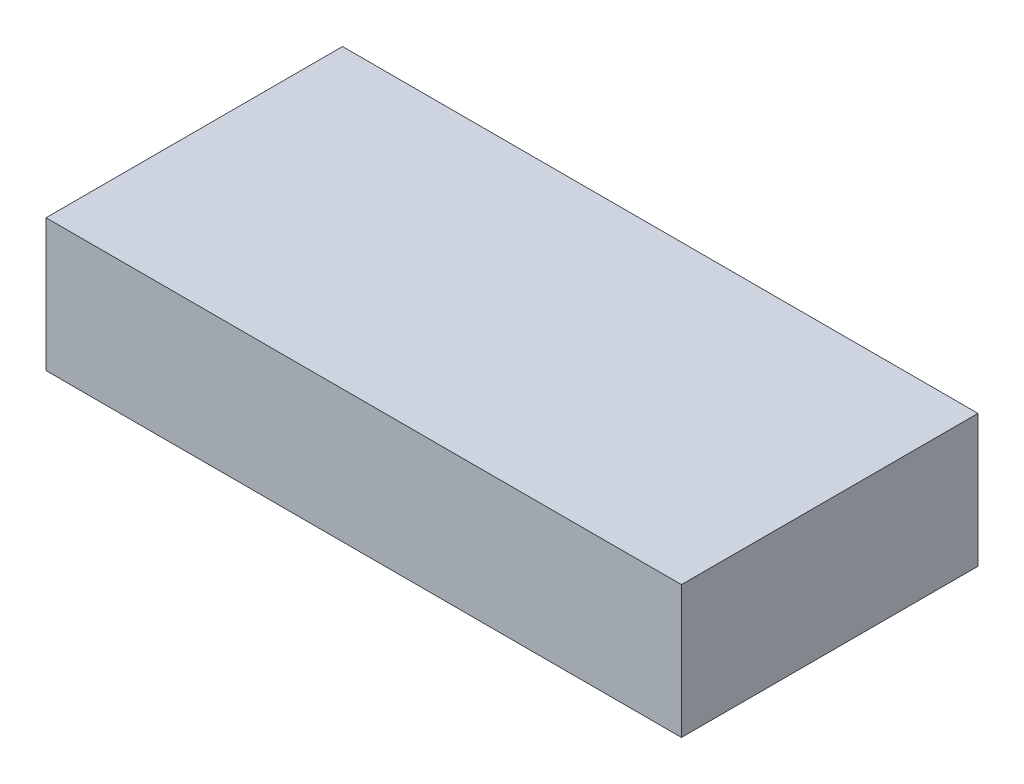
SolidWorks part; units mm, degrees
ref_plane "Front" through (0, 0, 0) normal (0, 0, 1) x (1, 0, 0)
ref_plane "Top" through (0, 0, 0) normal (0, 1, 0) x (1, 0, 0)
ref_plane "Right" through (0, 0, 0) normal (1, 0, 0) x (0, 0, -1)
sketch "Sketch1" plane through (0, 0, 0) normal (0, 1, 0) x (1, 0, 0)
  line L1 (0, 0) -> (120, 0)
  line L2 (0, 0) -> (0, 56)
  line L3 (0, 56) -> (120, 56)
  line L4 (120, 0) -> (120, 56)
  dimension "D1" = 120
  dimension "D2" = 56
extrude "Boss-Extrude1" add sketch "Sketch1" along normal blind 25
